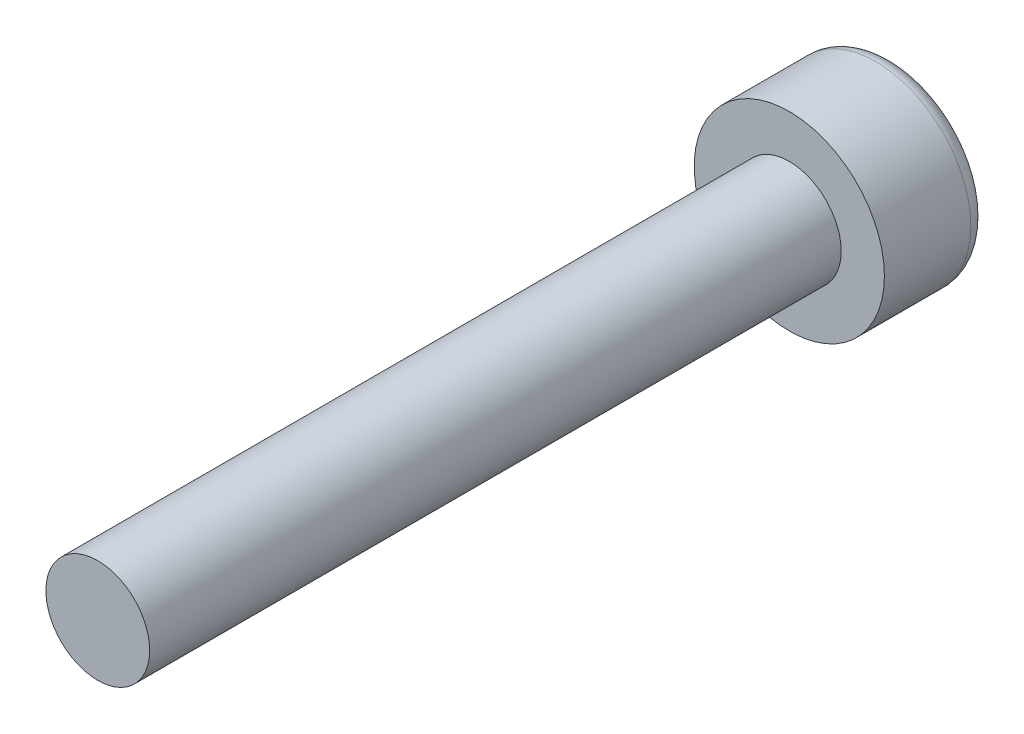
SolidWorks part; units mm, degrees
ref_plane "正面" through (0, 0, 0) normal (0, 0, 1) x (1, 0, 0)
ref_plane "平面" through (0, 0, 0) normal (0, 1, 0) x (1, 0, 0)
ref_plane "右側面" through (0, 0, 0) normal (1, 0, 0) x (0, 0, -1)
sketch "ｽｹｯﾁ2" plane through (0, 0, 0) normal (0, 0, 1) x (1, 0, 0)
  circle A0 centre (0, 0) radius 2.75
  dimension "D1" = 5.5
extrude "ﾎﾞｽ - 押し出し1" add sketch "ｽｹｯﾁ2" along normal blind 3
sketch "ｽｹｯﾁ3" plane through (0, 0, 3) normal (0, 0, 1) x (1, 0, 0)
  circle A0 centre (0, 0) radius 1.5
  dimension "D1" = 3
extrude "ﾎﾞｽ - 押し出し2" add sketch "ｽｹｯﾁ3" along normal blind 20
fillet "ﾌｨﾚｯﾄ1" radius 0.5 1 edges at (2.75, 0, 0)
